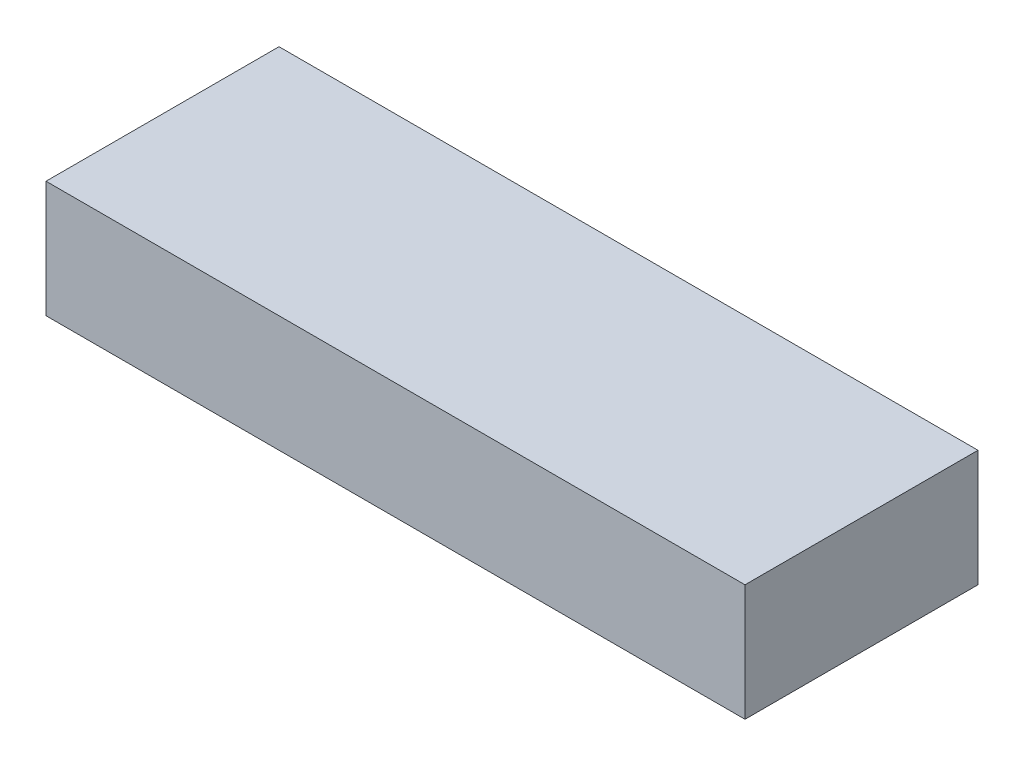
SolidWorks part; units mm, degrees
ref_plane "Front Plane" through (0, 0, 0) normal (0, 0, 1) x (1, 0, 0)
ref_plane "Top Plane" through (0, 0, 0) normal (0, 1, 0) x (1, 0, 0)
ref_plane "Right Plane" through (0, 0, 0) normal (1, 0, 0) x (0, 0, -1)
sketch "Sketch1" plane through (0, 0, 0) normal (0, 1, 0) x (1, 0, 0)
  line L1 (0, 0) -> (30, 0)
  line L2 (0, 0) -> (0, 10)
  line L3 (0, 10) -> (30, 10)
  line L4 (30, 0) -> (30, 10)
  dimension "D1" = 10
  dimension "D2" = 30
extrude "Boss-Extrude1" add sketch "Sketch1" along normal blind 5
